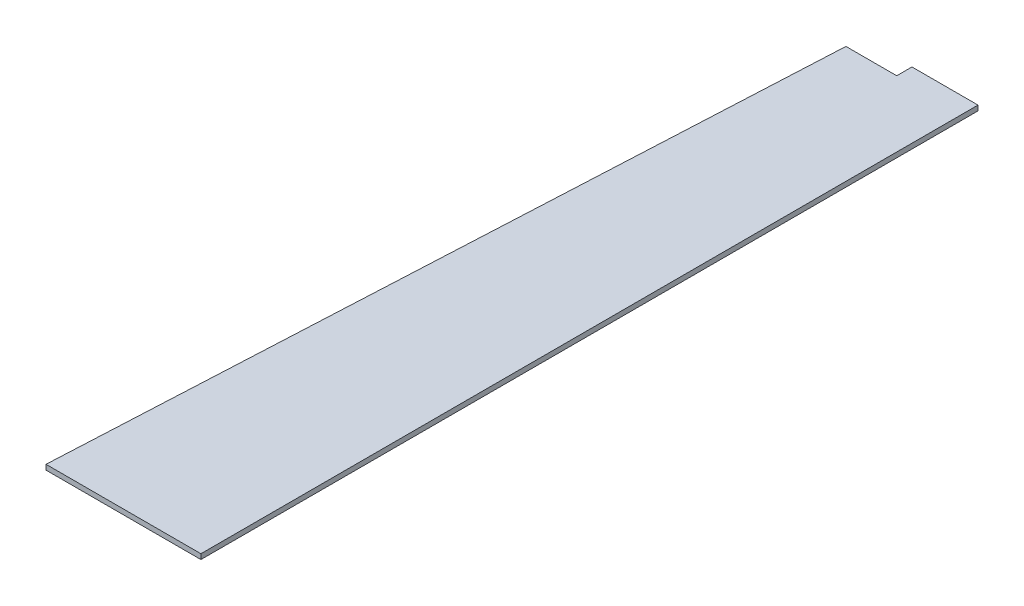
SolidWorks part; units mm, degrees
ref_plane "Face" through (0, 0, 0) normal (0, 0, 1) x (1, 0, 0)
ref_plane "Dessus" through (0, 0, 0) normal (0, 1, 0) x (1, 0, 0)
ref_plane "Droite" through (0, 0, 0) normal (1, 0, 0) x (0, 0, -1)
sketch "Esquisse1" plane through (0, 0, 0) normal (0, 1, 0) x (1, 0, 0)
  line L0 (0, 0) -> (0, 1500) construction
  line L1 (0, 1500) -> (630, 1500) construction
  line L2 (630, 1500) -> (630, 0) construction
  line L3 (630, 0) -> (0, 0) construction
  line L4 (325, 0) -> (400, 1500)
  line L5 (400, 1500) -> (500, 1500)
  line L6 (500, 1500) -> (500, 1530)
  line L7 (500, 1530) -> (630, 1530)
  line L8 (630, 1530) -> (630, 0)
  line L9 (630, 0) -> (325, 0)
  dimension "D1" = 1500
  dimension "D2" = 630
  dimension "D3" = 325
  dimension "D4" = 400
  dimension "D5" = 100
  dimension "D6" = 30
extrude "Extrusion1" add sketch "Esquisse1" along normal blind 10
